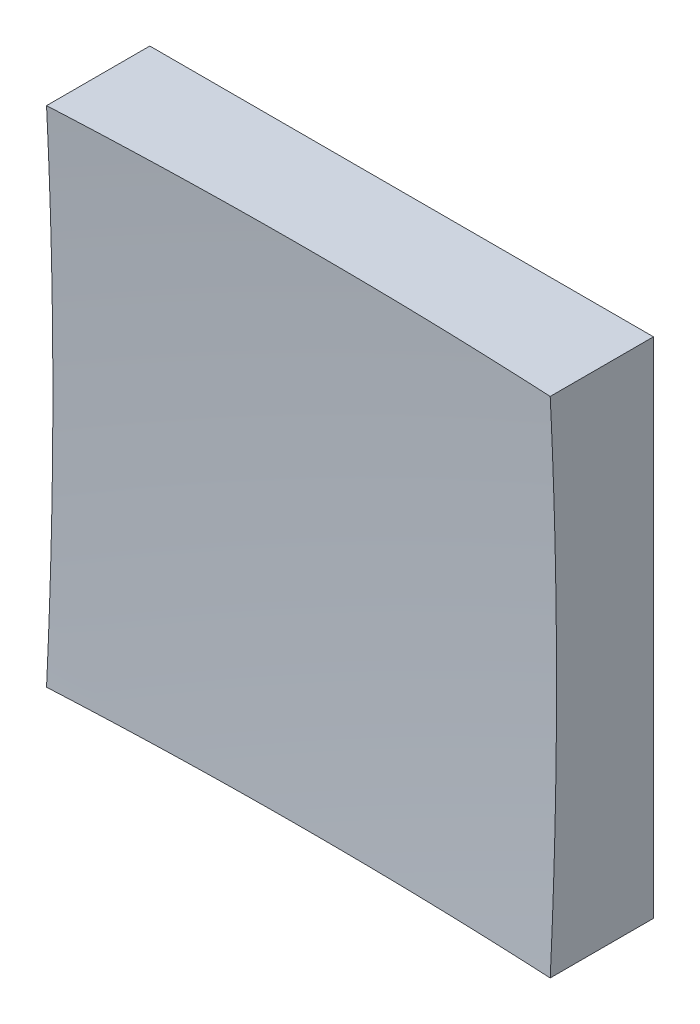
SolidWorks part; units mm, degrees
ref_plane "前视基准面" through (0, 0, 0) normal (0, 0, 1) x (1, 0, 0)
ref_plane "上视基准面" through (0, 0, 0) normal (0, 1, 0) x (1, 0, 0)
ref_plane "右视基准面" through (0, 0, 0) normal (1, 0, 0) x (0, 0, -1)
sketch "草图1" plane through (0, 0, 0) normal (0, 0, 1) x (1, 0, 0)
  line L1 (-25, 25) -> (25, 25)
  line L2 (-25, 25) -> (-25, -25)
  line L3 (-25, -25) -> (25, -25)
  line L4 (25, 25) -> (25, -25)
  line L5 (-25, 25) -> (25, -25) construction
  line L6 (-25, -25) -> (25, 25) construction
  point P0 (0, 0)
  dimension "D1" = 50
  dimension "D2" = 50
extrude "凸台-拉伸1" add sketch "草图1" along normal blind 50 contours L2 L3 L4 L1
sketch "草图2" plane through (0, 0, 0) normal (0, 1, 0) x (1, 0, 0)
  line L0 (-7.4603, -9) -> (7.3192, -9) construction
  line L1 (0, 0) -> (0, -12.1749) construction
  line L2 (487.4227, -397.5591) -> (0, -397.5591)
  line L3 (0, -397.5591) -> (0, -9)
  arc A1 (487.4227, -397.5591) -> (0, -9) centre (0, -509) ccw
  dimension "D2" = 1000
  dimension "D1" = 9
revolve "切除-旋转2" cut sketch "草图2" angle 360 about L3
